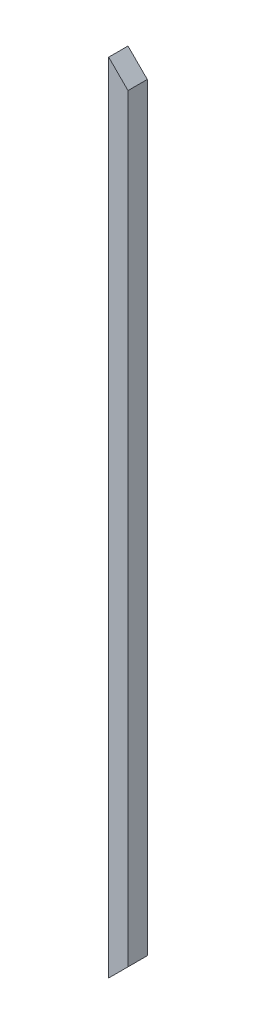
SolidWorks part; units mm, degrees
material "Oak"
ref_plane "Front Plane" through (0, 0, 0) normal (0, 0, 1) x (1, 0, 0)
ref_plane "Top Plane" through (0, 0, 0) normal (0, 1, 0) x (1, 0, 0)
ref_plane "Right Plane" through (0, 0, 0) normal (1, 0, 0) x (0, 0, -1)
sketch "Sketch1" plane through (0, 0, 0) normal (0, 1, 0) x (1, 0, 0)
  line L1 (-9.525, -9.525) -> (9.525, -9.525)
  line L2 (-9.525, -9.525) -> (-9.525, 9.525)
  line L3 (-9.525, 9.525) -> (9.525, 9.525)
  line L4 (9.525, -9.525) -> (9.525, 9.525)
  line L5 (-9.525, -9.525) -> (9.525, 9.525) construction
  line L6 (-9.525, 9.525) -> (9.525, -9.525) construction
  point P0 (0, 0)
  dimension "D1" = 19.05
extrude "Boss-Extrude1" add sketch "Sketch1" along normal blind 787.4
sketch "Sketch2" plane through (0, 0, -9.525) normal (0, 0, -1) x (-1, 0, 0)
  line L0 (9.525, 787.4) -> (-9.525, 768.35)
  line L1 (-9.525, 787.4) -> (-9.525, 0) construction
  line L2 (-9.525, 768.35) -> (-9.525, 787.4)
  line L3 (-9.525, 787.4) -> (9.525, 787.4)
  line L4 (9.525, 787.4) -> (9.525, 0) construction
  line L5 (9.525, 393.7) -> (-9.525, 393.7) construction
  line L6 (-9.525, 19.05) -> (-9.525, 0)
  line L7 (9.525, 0) -> (-9.525, 19.05)
  line L8 (-9.525, 0) -> (9.525, 0)
extrude "Cut-Extrude1" cut sketch "Sketch2" against normal through all
